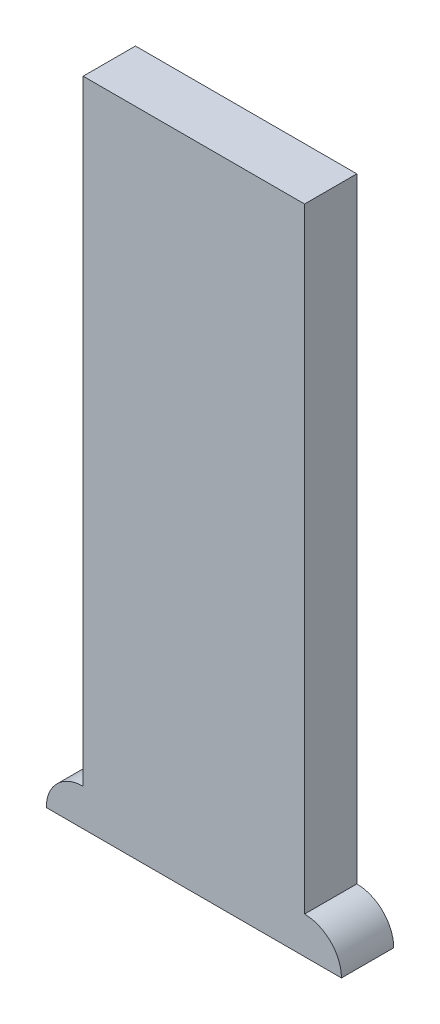
SolidWorks part; units mm, degrees
ref_plane "Front Plane" through (0, 0, 0) normal (0, 0, 1) x (1, 0, 0)
ref_plane "Top Plane" through (0, 0, 0) normal (0, 1, 0) x (1, 0, 0)
ref_plane "Right Plane" through (0, 0, 0) normal (1, 0, 0) x (0, 0, -1)
sketch "Sketch1" plane through (0, 0, 0) normal (0, 0, 1) x (1, 0, 0)
  line L0 (0, 0) -> (48, 0)
  line L1 (6, 6) -> (42, 6)
  arc A2 (0, 0) -> (6, 6) centre (6, 0) cw
  arc A3 (42, 6) -> (48, 0) centre (42, 0) cw
  point P6 (24, 6)
  dimension "D3" = 6
  dimension "D1" = 48
  dimension "D2" = 36
extrude "Boss-Extrude1" add sketch "Sketch1" along normal blind 8.5
sketch "Sketch2" plane through (0, 0, 0) normal (0, -1, 0) x (1, 0, 0)
  line L0 (24, 0) -> (24, 8.5) construction
  line L3 (0, 4.25) -> (48, 4.25) construction
  line L4 (0, 8.5) -> (0, 0) construction
  line L5 (48, 8.5) -> (48, 0) construction
  line L6 (0, 8.5) -> (48, 8.5) construction
  circle A0 centre (9, 4.25) radius 3.25
  circle A1 centre (39, 4.25) radius 3.25
  point P5 (24, 4.25)
  dimension "D2" = 6.5
  dimension "D1" = 15
sketch "Sketch5" plane through (0, 6, 0) normal (0, 1, 0) x (1, 0, 0)
  line L0 (24, -8.5) -> (24, 0) construction
  line L1 (42, -8.5) -> (42, 0)
  line L2 (42, 0) -> (6, 0)
  line L3 (6, 0) -> (6, -8.5)
  line L4 (6, -8.5) -> (42, -8.5)
  circle A0 centre (39, -4.25) radius 1.75 construction
  circle A1 centre (9, -4.25) radius 1.75 construction
  dimension "D1" = 3.5
extrude "Boss-Extrude2" add sketch "Sketch5" along normal blind 100
sketch "Sketch12" plane through (0, 0, 0) normal (0, 0, -1) x (-1, 0, 0)
  line L0 (-42, 106) -> (-42, 6) construction
  line L1 (-42, 106) -> (-6, 106) construction
  circle A0 centre (-37, 101) radius 1.5
  dimension "D1" = 3
  dimension "D2" = 5
  dimension "D3" = 5
ref_plane "Plane1" through (24, 0, 0) normal (1, 0, 0) x (0, 0, -1)
hole_wizard "Ø3.0mm Dowel Hole3" positions "Sketch15" profile "Sketch14" hole size "Ø3.0" standard "ANSI Metric"
sketch "Sketch15" plane through (0, 0, 0) normal (0, 0, -1) x (-1, 0, 0)
  point P0 (-37, 101)
sketch "Sketch14" plane through (37, 101, 0) normal (1, 0, 0) x (0, 1, 0)
  line L0 (0, 0) -> (0, 5.9013)
  line L1 (0, 5.9013) -> (1.5, 5)
  line L2 (1.5, 5) -> (1.5, 0)
  line L5 (1.5, 0) -> (0, 0)
  line L10 (0, 5.9013) -> (-1.5, 5) construction
  line L11 (0, -6.35) -> (0, 107.95) construction
  dimension "Hole Dia." = 3
  dimension "Hole Depth" = 5
  dimension "Drill Angle" = 118
hole_wizard "CSK for M3 Flat Head Machine Screw2" positions "Sketch16" profile "Sketch17" countersink size "M3" standard "ANSI Metric"
sketch "Sketch16" plane through (0, 0, 0) normal (0, -1, 0) x (-1, 0, 0)
  point P0 (-39, -4.25)
  point P3 (-9, -4.25)
sketch "Sketch17" plane through (39, 0, 4.25) normal (1, 0, 0) x (0, 0, -1)
  line L0 (0, 0) -> (0, 11.0215)
  line L1 (0, 11.0215) -> (1.7, 10)
  line L2 (1.7, 10) -> (1.7, 1.45)
  line L3 (1.7, 1.45) -> (3.15, 0)
  line L5 (3.15, 0) -> (0, 0)
  line L6 (-1.7, 1.45) -> (-3.15, 0) construction
  line L10 (0, 11.0215) -> (-1.7, 10) construction
  line L11 (0, -6.35) -> (0, 107.95) construction
  dimension "Hole Dia." = 3.4
  dimension "Hole Depth" = 10
  dimension "Near C'Sink Dia." = 6.3
  dimension "Near C'Sink Angle" = 90
  dimension "Drill Angle" = 118
mirror "Mirror1" about plane through (24, 0, 0) normal (1, 0, 0) of "Ø3.0mm Dowel Hole3"
pattern_linear "LPattern1" count 12 spacing 8 along (0, -1, 0) of "Mirror1", "Ø3.0mm Dowel Hole3"
